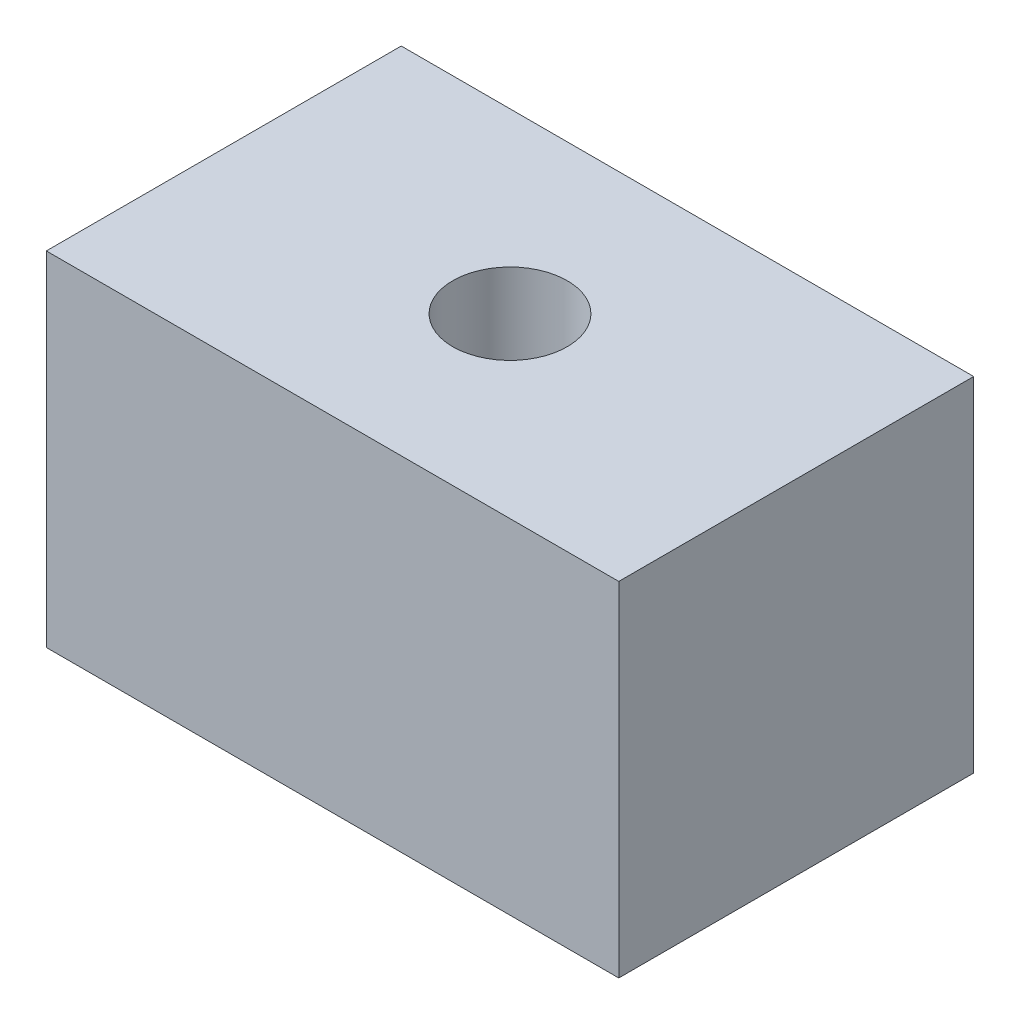
SolidWorks part; units mm, degrees
ref_plane "Front Plane" through (0, 0, 0) normal (0, 0, 1) x (1, 0, 0)
ref_plane "Top Plane" through (0, 0, 0) normal (0, 1, 0) x (1, 0, 0)
ref_plane "Right Plane" through (0, 0, 0) normal (1, 0, 0) x (0, 0, -1)
sketch "Sketch1" plane through (0, 0, 0) normal (0, 1, 0) x (1, 0, 0)
  line L1 (-12.5, -7.75) -> (12.5, -7.75)
  line L2 (-12.5, -7.75) -> (-12.5, 7.75)
  line L3 (-12.5, 7.75) -> (12.5, 7.75)
  line L4 (12.5, -7.75) -> (12.5, 7.75)
  line L5 (-12.5, -7.75) -> (12.5, 7.75) construction
  line L6 (-12.5, 7.75) -> (12.5, -7.75) construction
  point P0 (0, 0)
  dimension "D1" = 25
  dimension "D2" = 15.5
extrude "Boss-Extrude1" add sketch "Sketch1" along normal blind 15
sketch "Sketch2" plane through (0, 15, 0) normal (0, 1, 0) x (1, 0, 0)
  circle A0 centre (0, 0) radius 2.5
  dimension "D1" = 5
extrude "Cut-Extrude1" cut sketch "Sketch2" against normal blind 10
sketch "Sketch4" plane through (0, 0, 0) normal (0, -1, 0) x (1, 0, 0)
  circle A0 centre (5, 0) radius 2.5
  point P2 (0, 0)
  point P4 (0, 0)
  point P5 (0, 0)
  point P6 (0, 0)
  point P7 (0, 0)
  dimension "D1" = 5
sketch "Sketch5" plane through (0, 0, 0) normal (0, -1, 0) x (1, 0, 0)
  circle A0 centre (-5, 0) radius 2.5
  point P2 (0, 0)
  point P4 (0, 0)
  point P5 (0, 0)
  point P6 (0, 0)
  dimension "D1" = 10
extrude "Cut-Extrude3" cut sketch "Sketch4" against normal blind 4 contours A0
extrude "Cut-Extrude4" cut sketch "Sketch5" against normal blind 4 contours A0
